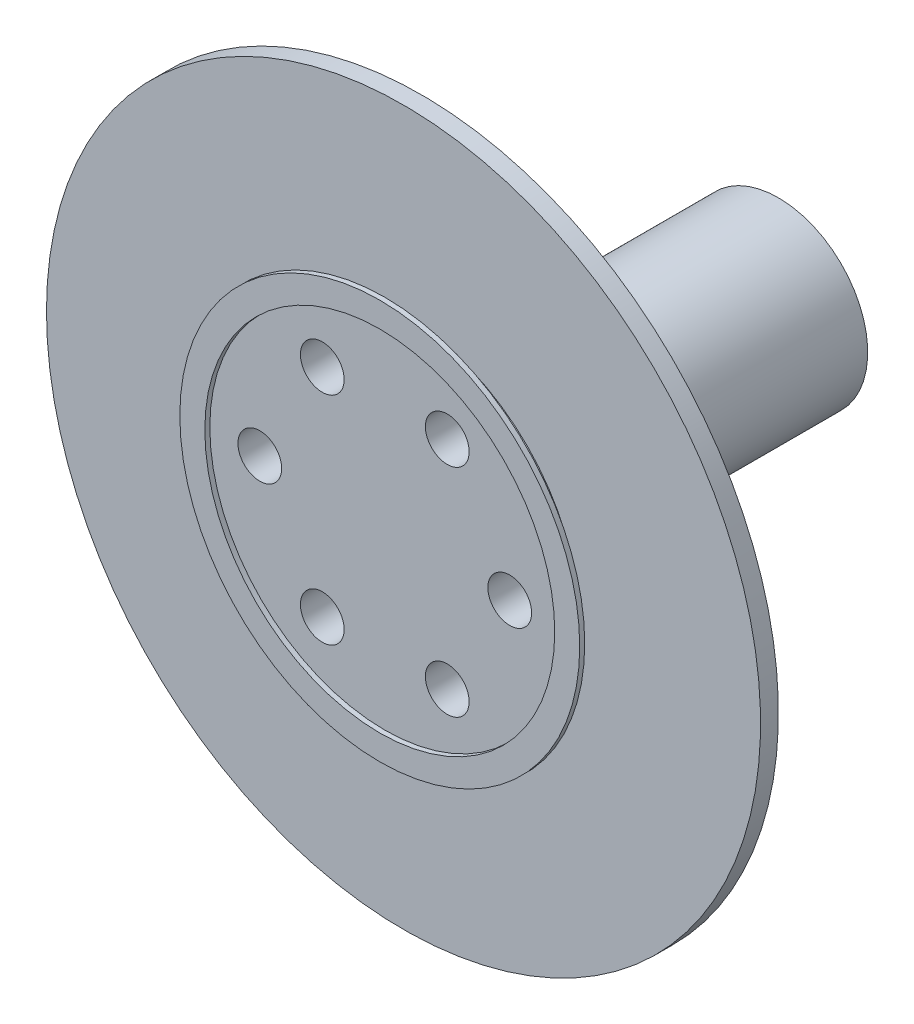
SolidWorks part; units mm, degrees
ref_plane "前视基准面" through (0, 0, 0) normal (0, 0, 1) x (1, 0, 0)
ref_plane "上视基准面" through (0, 0, 0) normal (0, 1, 0) x (1, 0, 0)
ref_plane "右视基准面" through (0, 0, 0) normal (1, 0, 0) x (0, 0, -1)
sketch "草图1" plane through (0, 0, 0) normal (0, 0, 1) x (1, 0, 0)
  circle A0 centre (0, 0) radius 15
  dimension "D1" = 30
extrude "拉伸-薄壁1" add sketch "草图1" along normal blind 0.4 thin thin type mid plane wall 2
sketch "草图2" plane through (0, 0, 0) normal (0, 0, -1) x (-1, 0, 0)
  circle A0 centre (0, 0) radius 14
  circle A1 centre (0, 0) radius 14 construction
extrude "凸台-拉伸1" add sketch "草图2" along normal blind 1.5
sketch "草图3" plane through (0, 0, 0) normal (0, 0, 1) x (1, 0, 0)
  circle A0 centre (10, 0) radius 1.75
  circle A1 centre (5, -8.6603) radius 1.75
  circle A2 centre (-5, -8.6603) radius 1.75
  circle A3 centre (-10, 0) radius 1.75
  circle A4 centre (-5, 8.6603) radius 1.75
  circle A5 centre (5, 8.6603) radius 1.75
  point P15 (0, 0)
  dimension "D1" = 3.5
  dimension "D2" = 10
  dimension "D3" = 6
extrude "切除-拉伸1" cut sketch "草图3" against normal up to surface (1.5 mm away) up to face at (-14, 0, -1.5)
scale "缩放比例1" bodies to scale 106 110 scale about origin uniform scaling yes scale factor 0.35
sketch "草图4" plane through (0, 0, -0.525) normal (0, 0, -1) x (-1, 0, 0)
  circle A0 centre (0, 0) radius 10
  circle A1 centre (1.75, -3.0311) radius 0.6125
  circle A2 centre (1.75, -3.0311) radius 0.6125 construction
  circle A3 centre (-1.75, -3.0311) radius 0.6125
  circle A4 centre (-3.5, 0) radius 0.6125
  circle A5 centre (-1.75, 3.0311) radius 0.6125
  circle A6 centre (1.75, 3.0311) radius 0.6125
  circle A7 centre (3.5, 0) radius 0.6125
  point P19 (0, 0)
  dimension "D1" = 20
  dimension "D2" = 6
extrude "凸台-拉伸2" add sketch "草图4" along normal blind 0.5
sketch "草图5" plane through (0, 0, -1.025) normal (0, 0, -1) x (-1, 0, 0)
  line L0 (-1.249, 1) -> (1.249, 1)
  circle A0 centre (0, 0) radius 2.5
  arc A1 (-1.249, 1) -> (1.249, 1) centre (0, 0) ccw
  dimension "D1" = 5
  dimension "D2" = 3.2
  dimension "D3" = 1
extrude "凸台-拉伸3" add sketch "草图5" along normal blind 10
